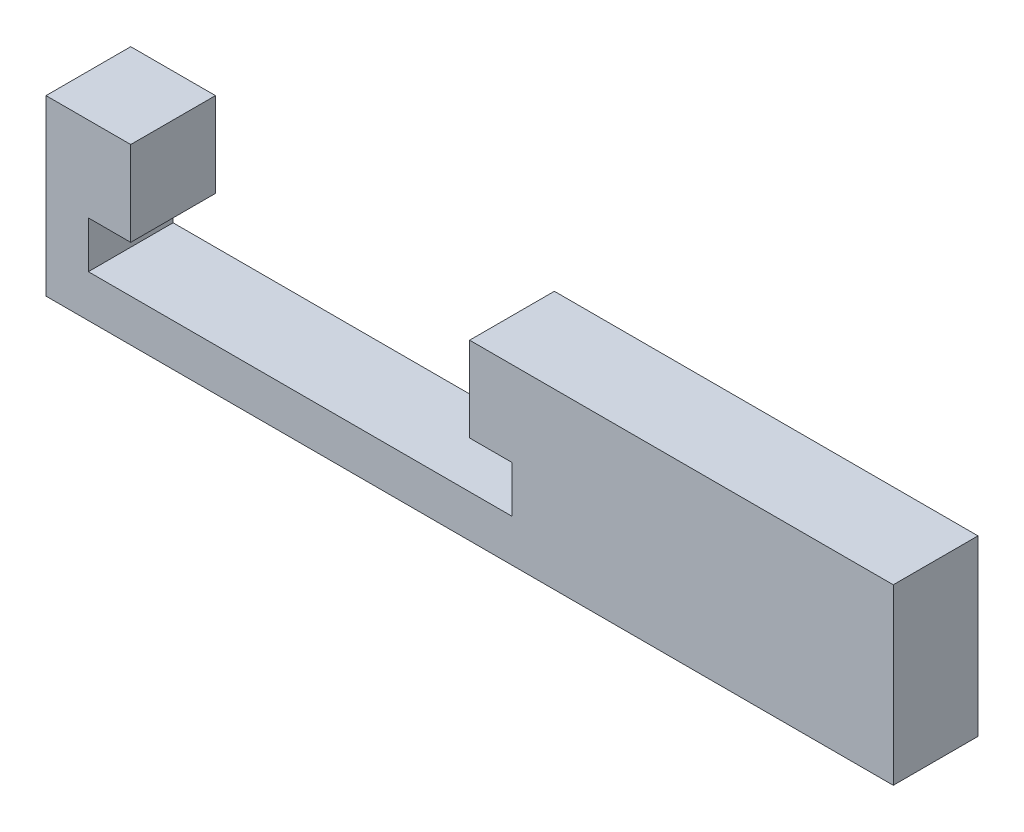
SolidWorks part; units mm, degrees
ref_plane "Front Plane" through (0, 0, 0) normal (0, 0, 1) x (1, 0, 0)
ref_plane "Top Plane" through (0, 0, 0) normal (0, 1, 0) x (1, 0, 0)
ref_plane "Right Plane" through (0, 0, 0) normal (1, 0, 0) x (0, 0, -1)
sketch "Sketch1" plane through (0, 0, 0) normal (0, 0, 1) x (1, 0, 0)
  line L0 (-12.7, 0) -> (12.7, 0)
  line L1 (-12.7, 0) -> (-12.7, 2.794)
  line L2 (-12.7, 2.794) -> (-10.16, 2.794)
  line L3 (-10.16, 2.794) -> (-10.16, 7.874)
  line L4 (-10.16, 7.874) -> (-15.24, 7.874)
  line L5 (-15.24, 7.874) -> (-15.24, -2.54)
  line L6 (-15.24, -2.54) -> (15.24, -2.54)
  line L7 (0, 0) -> (0, -2.54) construction
  line L9 (10.16, 7.874) -> (15.24, 7.874)
  line L10 (10.16, 2.794) -> (10.16, 7.874)
  line L11 (12.7, 2.794) -> (10.16, 2.794)
  line L12 (12.7, 0) -> (12.7, 2.794)
  line L13 (15.24, 7.874) -> (35.56, 7.874)
  line L14 (35.56, 7.874) -> (35.56, -2.54)
  line L15 (35.56, -2.54) -> (15.24, -2.54)
  point P15 (0, 0)
  point P19 (15.6552, 3.3748)
  point P20 (15.6552, 5.08)
  dimension "D1" = 25.4
  dimension "D2" = 2.794
  dimension "D3" = 2.54
  dimension "D4" = 5.08
  dimension "D5" = 2.54
  dimension "D6" = 2.54
  dimension "D7" = 20.32
extrude "Boss-Extrude1" add sketch "Sketch1" along normal blind 5.08 contours L12 L11 L10 L9 L13 L14 L15 L6 L5 L4 L3 L2 L1 L0
